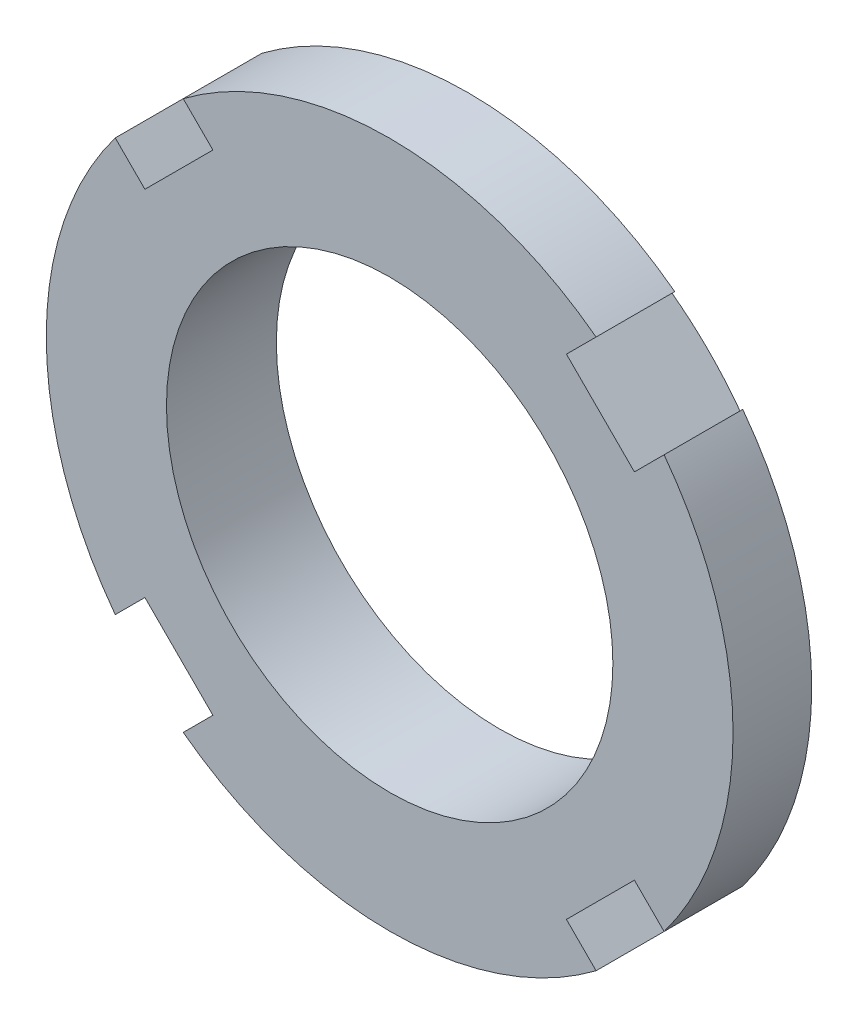
SolidWorks part; units mm, degrees
material "Alloy Steel"
ref_plane "Front Plane" through (0, 0, 0) normal (0, 0, 1) x (1, 0, 0)
ref_plane "Top Plane" through (0, 0, 0) normal (0, 1, 0) x (1, 0, 0)
ref_plane "Right Plane" through (0, 0, 0) normal (1, 0, 0) x (0, 0, -1)
sketch "Sketch1" plane through (0, 0, 0) normal (0, 0, 1) x (1, 0, 0)
  circle A0 centre (0, 0) radius 25
  circle A1 centre (0, 0) radius 16.25
  dimension "D1" = 50
  dimension "D2" = 32.5
extrude "Extrude1" add sketch "Sketch1" along normal blind 8
sketch "Sketch2" plane through (0, 0, 8) normal (0, 0, 1) x (1, 0, 0)
  line L0 (0, 0) -> (22.7176, 0) construction
  line L1 (0, 0) -> (15.6425, 15.6425) construction
  line L2 (15.0287, 19.9784) -> (12.8693, 17.8191)
  line L3 (12.8693, 17.8191) -> (17.8191, 12.8693)
  line L4 (19.9784, 15.0287) -> (17.8191, 12.8693)
  arc A1 (19.9784, 15.0287) -> (15.0287, 19.9784) centre (0, 0) ccw
  circle A3 centre (0, 0) radius 25 construction
  dimension "D3" = 21.7
  dimension "D1" = 45
  dimension "D2" = 7
extrude "Cut-Extrude1" cut sketch "Sketch2" against normal through all
pattern_circular "CirPattern1" count 4 over 360 about axis through (0, 0, 0) along (0, 0, 1) of "Cut-Extrude1"
sketch "Sketch3" plane through (0, 0, 0) normal (0, 1, 0) x (1, 0, 0)
  line L0 (25, 0) -> (19.9784, 0) construction
  line L1 (25, -8) -> (25, 0) construction
  line L2 (25, 0) -> (21.5, 0)
  line L3 (25, -2.2729) -> (25, 0)
  line L4 (21.5, 0) -> (25, -2.2729)
  line L5 (0, 0) -> (0, 7.6185) construction
  dimension "D1" = 43
  dimension "D2" = 33
revolve "Cut-Revolve1" cut sketch "Sketch3" angle 360 about L5
